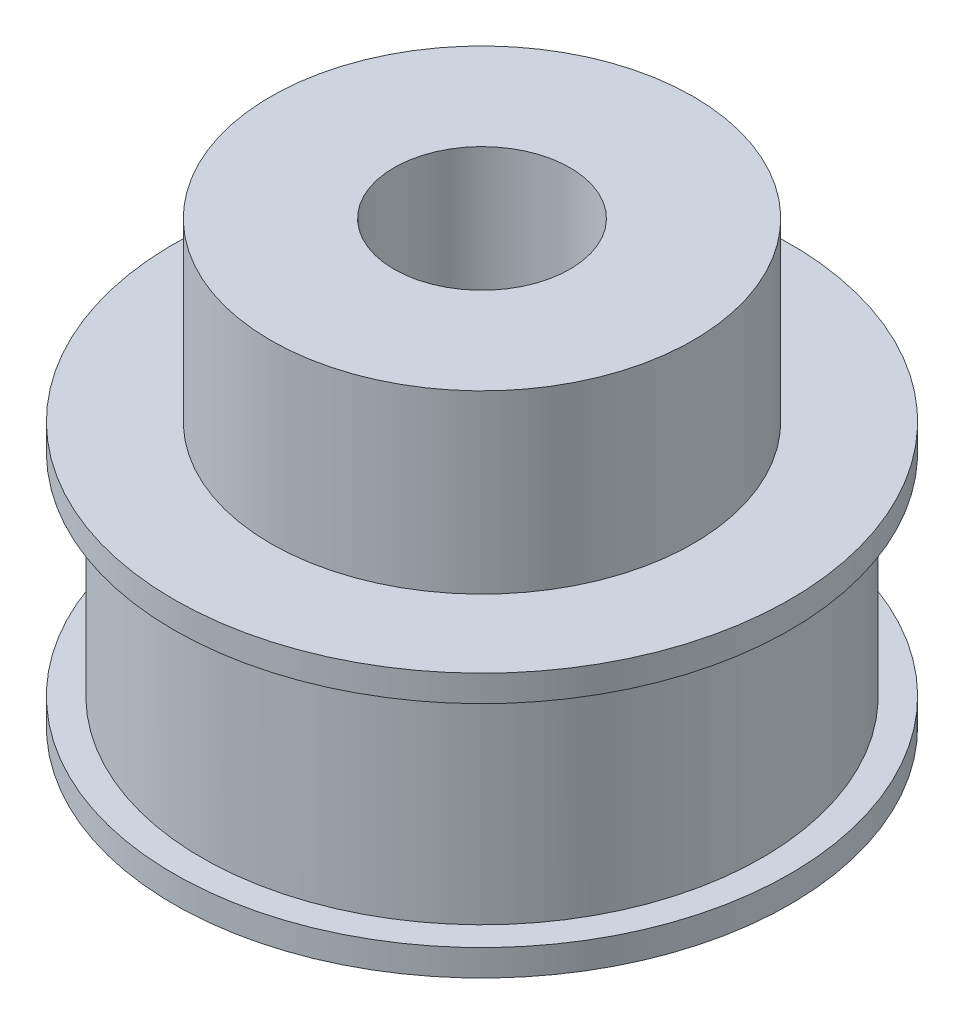
SolidWorks part; units mm, degrees
material "7079 Alloy"
ref_plane "Front Plane" through (0, 0, 0) normal (0, 0, 1) x (1, 0, 0)
ref_plane "Top Plane" through (0, 0, 0) normal (0, 1, 0) x (1, 0, 0)
ref_plane "Right Plane" through (0, 0, 0) normal (1, 0, 0) x (0, 0, -1)
sketch "Sketch1" plane through (0, 0, 0) normal (0, 1, 0) x (1, 0, 0)
  circle A0 centre (0, 0) radius 24.255
  dimension "D1" = 48.51
extrude "Boss-Extrude1" add sketch "Sketch1" along normal blind 15
sketch "Sketch2" plane through (0, 15, 0) normal (0, 1, 0) x (1, 0, 0)
  circle A0 centre (0, 0) radius 12
  dimension "D1" = 24
extrude "Boss-Extrude2" add sketch "Sketch2" along normal blind 10
sketch "Sketch3" plane through (0, 25, 0) normal (0, 1, 0) x (1, 0, 0)
  circle A0 centre (0, 0) radius 5
  dimension "D1" = 10
extrude "Cut-Extrude1" cut sketch "Sketch3" against normal blind 26
sketch "Sketch4" plane through (0, 0, 0) normal (0, -1, 0) x (1, 0, 0)
  circle A0 centre (0, 0) radius 15.915
  circle A2 centre (0, 0) radius 24.255
  circle A3 centre (0, 0) radius 24.255
  dimension "D1" = 31.83
  dimension "D2" = 0
extrude "Cut-Extrude3" cut sketch "Sketch4" against normal blind 15
sketch "Sketch5" plane through (0, 0, 0) normal (0, -1, 0) x (1, 0, 0)
  circle A0 centre (0, 0) radius 17.5
  circle A1 centre (0, 0) radius 15.915 construction
  circle A2 centre (0, 0) radius 15.915
  dimension "D1" = 35
extrude "Boss-Extrude3" add sketch "Sketch5" against normal blind 1.5
sketch "Sketch6" plane through (0, 15, 0) normal (0, 1, 0) x (1, 0, 0)
  circle A0 centre (0, 0) radius 17.5
  circle A1 centre (0, 0) radius 15.915 construction
  circle A2 centre (0, 0) radius 15.915
  dimension "D1" = 35
extrude "Boss-Extrude4" add sketch "Sketch6" against normal blind 1.5
scale "Scale1" scale about centroid uniform scaling yes scale factor 1.5
